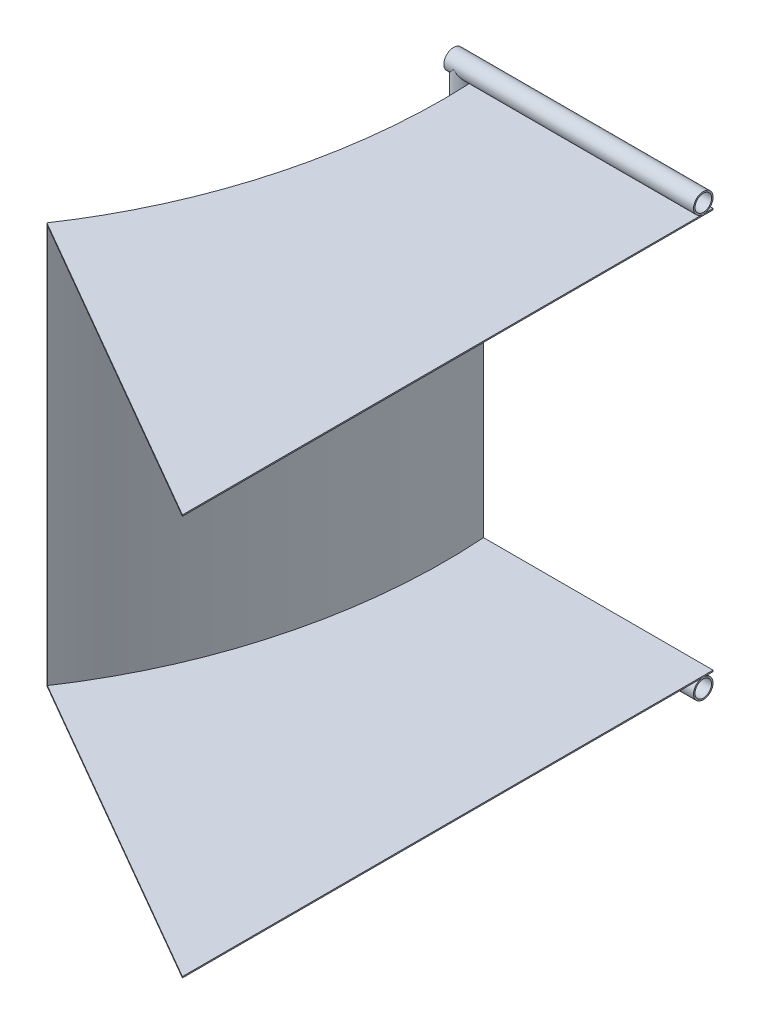
SolidWorks part; units mm, degrees
material "6061-T6 (SS)"
ref_plane "Front" through (0, 0, 0) normal (0, 0, 1) x (1, 0, 0)
ref_plane "Top" through (0, 0, 0) normal (0, 1, 0) x (1, 0, 0)
ref_plane "Right" through (0, 0, 0) normal (1, 0, 0) x (0, 0, -1)
sketch "Sketch1" plane through (0, 0, 0) normal (0, 1, 0) x (1, 0, 0)
  line L0 (0, 0) -> (0, 430)
  line L1 (0, 430) -> (-187, 430)
  line L2 (0, 0) -> (-359.5668, 0) construction
  line L3 (0, 0) -> (-259.8076, 150)
  spline S0 degree 3 poles (-187, 430) (-180.0493, 332.3329) (-204.7989, 231.6898) (-259.8076, 150) knots 0 0 0 0 1 1 1 1
  dimension "D1" = 30
extrude "Boss-Extrude1" add sketch "Sketch1" along normal blind 325
shell "Shell1" thickness 1.016
ref_plane "Plane1" through (0, 0, 0) normal (1, 0, 0) x (0, 0, -1)
sketch "Sketch2" plane through (0, 0, 0) normal (1, 0, 0) x (0, 0, -1)
  circle A0 centre (422.0625, 332.9375) radius 7.9375
extrude "Boss-Extrude2" add sketch "Sketch2" against normal blind 202.3 separate body
sketch "Sketch3" plane through (0, 0, 0) normal (1, 0, 0) x (0, 0, -1)
  circle A1 centre (422.0625, 332.9375) radius 6.6929
extrude "Cut-Extrude1" cut sketch "Sketch3" against normal through all
ref_plane "Plane2" through (0, 325, 0) normal (0, 1, 0) x (-1, 0, 0)
sketch "Sketch4" plane through (0, 325, 0) normal (0, 1, 0) x (-1, 0, 0)
  circle A0 centre (194.354, -422.0191) radius 7.9375
  circle A1 centre (194.354, -422.0191) radius 6.6929
extrude "Boss-Extrude3" add sketch "Sketch4" against normal blind 340.875 and the other way blind 15.875
sketch "Sketch6" plane through (0, 0, 0) normal (1, 0, 0) x (0, 0, -1)
  circle A0 centre (422.0114, -7.8887) radius 7.9375
  circle A1 centre (422.0114, -7.8887) radius 6.6929
  dimension "D1" = 1.2446
extrude "Boss-Extrude9" add sketch "Sketch6" along normal blind 0.0001 and the other way blind 202.3 separate body
sketch "Sketch7" plane through (0, 0, 0) normal (1, 0, 0) x (0, 0, -1)
  line L0 (414.125, 332.9375) -> (402.2163, 332.9375)
  line L1 (402.2163, 332.9375) -> (402.2163, 354.1563)
  line L2 (402.2163, 354.1563) -> (446.9272, 354.1563)
  line L3 (446.9272, 354.1563) -> (446.9272, 332.9375)
  line L4 (446.9272, 332.9375) -> (430, 332.9375)
  line L5 (414.0739, -7.8887) -> (410.0639, -7.8887)
  line L6 (410.0639, -7.8887) -> (410.0639, -17.849)
  line L7 (410.0639, -17.849) -> (432.9032, -17.849)
  line L8 (432.9032, -17.849) -> (432.9032, -7.8887)
  line L9 (432.9032, -7.8887) -> (429.9489, -7.8887)
  circle A0 centre (422.0625, 332.9375) radius 7.9375 construction
  arc A2 (414.125, 332.9375) -> (430, 332.9375) centre (422.0625, 332.9375) ccw
  circle A3 centre (422.0114, -7.8887) radius 7.9375 construction
  arc A4 (429.9489, -7.8887) -> (414.0739, -7.8887) centre (422.0114, -7.8887) ccw
extrude "Cut-Extrude2" cut sketch "Sketch7" against normal through all
